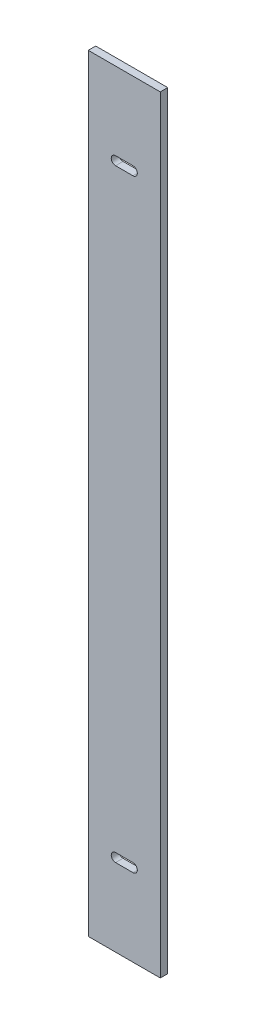
SolidWorks part; units mm, degrees
ref_plane "Plan de face" through (0, 0, 0) normal (0, 0, 1) x (1, 0, 0)
ref_plane "Plan de dessus" through (0, 0, 0) normal (0, 1, 0) x (1, 0, 0)
ref_plane "Plan de droite" through (0, 0, 0) normal (1, 0, 0) x (0, 0, -1)
sketch "Esquisse1" plane through (0, 0, 0) normal (0, 0, 1) x (1, 0, 0)
  line L0 (0, 154.5) -> (0, -154.5) construction
  line L1 (14.5, 154.5) -> (-14.5, 154.5)
  line L2 (14.5, 154.5) -> (14.5, -154.5)
  line L3 (14.5, -154.5) -> (-14.5, -154.5)
  line L4 (-14.5, 154.5) -> (-14.5, -154.5)
  line L5 (14.5, 154.5) -> (-14.5, -154.5) construction
  line L6 (14.5, -154.5) -> (-14.5, 154.5) construction
  line L7 (-14.5, 0) -> (14.5, 0) construction
  line L8 (-3.5, 121.5) -> (3.5, 121.5) construction
  line L9 (-3.5, 123.25) -> (3.5, 123.25)
  line L10 (-3.5, 119.75) -> (3.5, 119.75)
  line L14 (-3.5, -121.5) -> (3.5, -121.5) construction
  line L15 (-3.5, -123.25) -> (3.5, -123.25)
  line L16 (-3.5, -119.75) -> (3.5, -119.75)
  circle A0 centre (0, 121.5) radius 1.75 construction
  circle A1 centre (0, -121.5) radius 1.75 construction
  arc A2 (-3.5, 123.25) -> (-3.5, 119.75) centre (-3.5, 121.5) ccw
  arc A3 (3.5, 119.75) -> (3.5, 123.25) centre (3.5, 121.5) ccw
  arc A6 (-3.5, -123.25) -> (-3.5, -119.75) centre (-3.5, -121.5) cw
  arc A7 (3.5, -119.75) -> (3.5, -123.25) centre (3.5, -121.5) cw
  point P0 (0, 0)
  point P16 (0, 121.5)
  point P31 (0, -121.5)
  dimension "D3" = 3.5
  dimension "D6" = 1.75
  dimension "D1" = 29
  dimension "D2" = 309
  dimension "D4" = 33
  dimension "D5" = 7
extrude "Boss.-Extru.1" add sketch "Esquisse1" along normal blind 3
